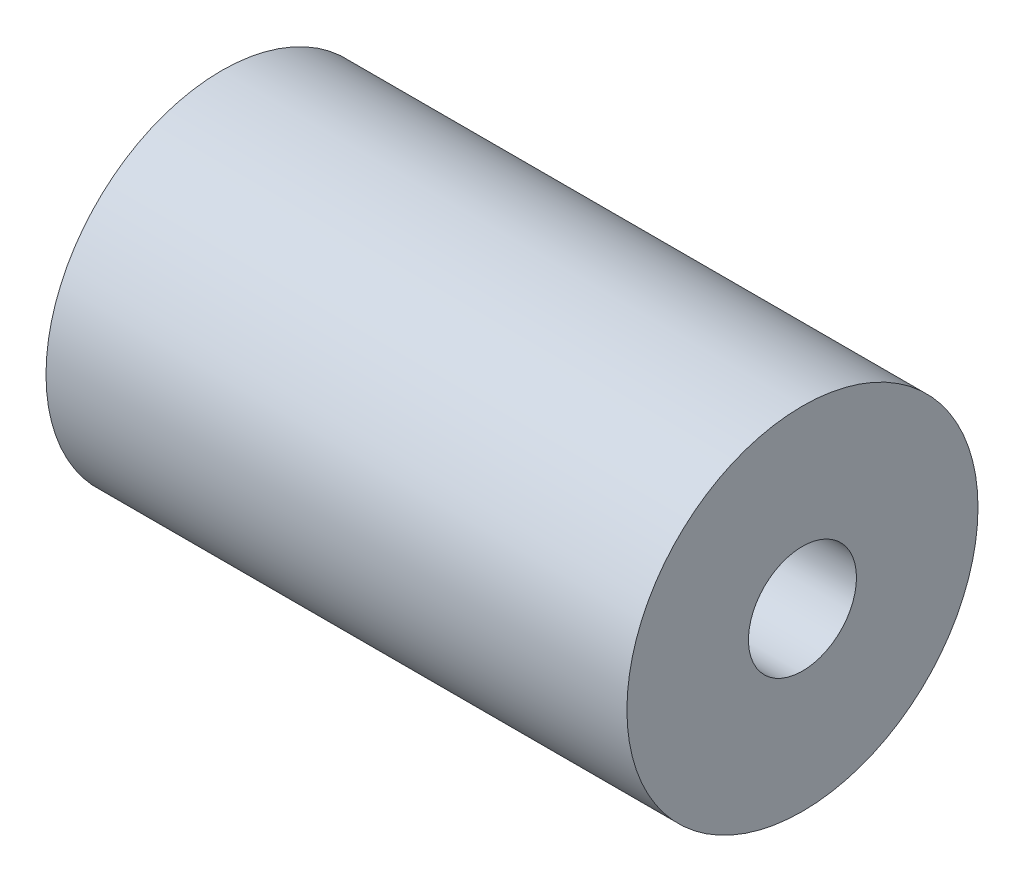
SolidWorks part; units mm, degrees
ref_plane "Front Plane" through (0, 0, 0) normal (0, 0, 1) x (1, 0, 0)
ref_plane "Top Plane" through (0, 0, 0) normal (0, 1, 0) x (1, 0, 0)
ref_plane "Right Plane" through (0, 0, 0) normal (1, 0, 0) x (0, 0, -1)
sketch "Sketch1" plane through (0, 0, 0) normal (1, 0, 0) x (0, 0, -1)
  circle A0 centre (0, 0) radius 2
  circle A1 centre (0, 0) radius 6.5
  dimension "D1" = 4
  dimension "D2" = 13
extrude "Boss-Extrude1" add sketch "Sketch1" along normal blind 21.51
